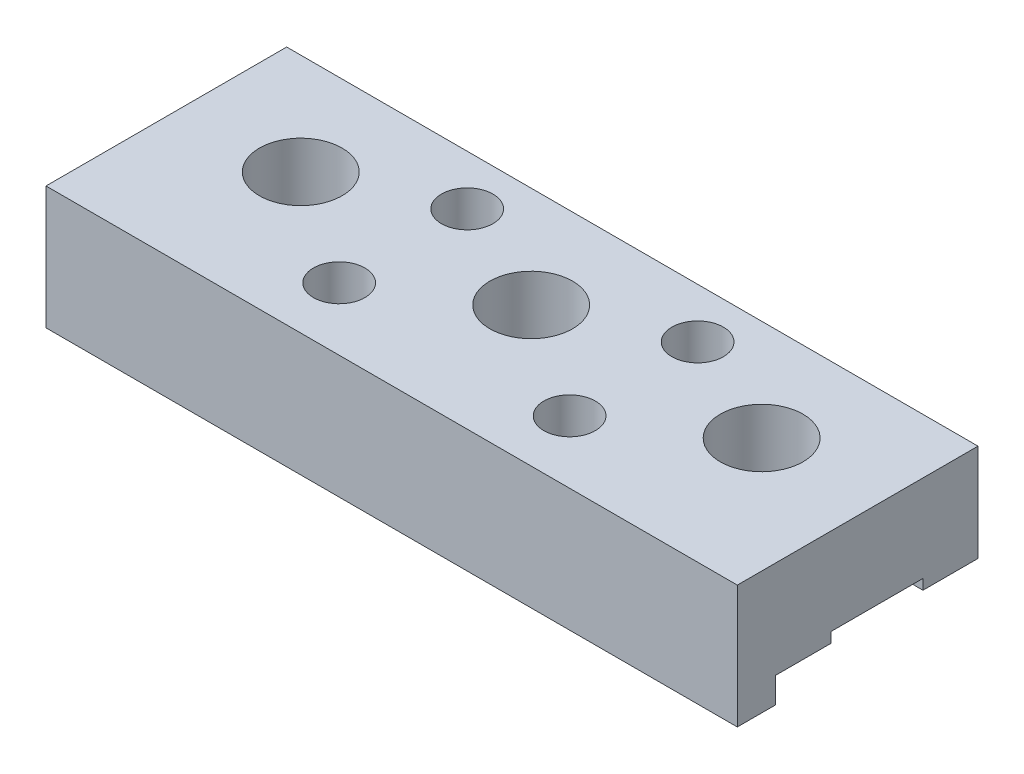
SolidWorks part; units mm, degrees
material "304 SSTL"
ref_plane "Front" through (0, 0, 0) normal (0, 0, 1) x (1, 0, 0)
ref_plane "Top" through (0, 0, 0) normal (0, 1, 0) x (1, 0, 0)
ref_plane "Right" through (0, 0, 0) normal (1, 0, 0) x (0, 0, -1)
sketch "Sketch1" plane through (0, 0, 0) normal (0, 1, 0) x (1, 0, 0)
  line L1 (-34.29, 11.43) -> (34.29, 11.43)
  line L2 (-34.29, 11.43) -> (-34.29, -11.43)
  line L3 (-34.29, -11.43) -> (34.29, -11.43)
  line L4 (34.29, 11.43) -> (34.29, -11.43)
  line L5 (-34.29, 11.43) -> (34.29, -11.43) construction
  line L6 (-34.29, -11.43) -> (34.29, 11.43) construction
  point P0 (0, 0)
  dimension "D1" = 68.58
  dimension "D2" = 22.86
extrude "Extrude1" add sketch "Sketch1" along normal blind 9.652
sketch "Sketch4" plane through (0, 9.652, 0) normal (0, 1, 0) x (1, 0, 0)
  line L0 (-34.29, 11.43) -> (-34.29, -11.43) construction
  line L1 (-34.29, -9.9822) -> (34.29, -9.9822)
  line L2 (-34.29, -9.9822) -> (-34.29, -13.7922)
  line L3 (-34.29, -13.7922) -> (34.29, -13.7922)
  line L4 (34.29, -9.9822) -> (34.29, -13.7922)
  line L5 (34.29, -11.43) -> (34.29, 11.43) construction
  line L6 (-34.29, -11.43) -> (34.29, -11.43) construction
  dimension "D1" = 1.4478
  dimension "D2" = 3.81
extrude "Extrude3" add sketch "Sketch4" against normal offset from surface (12.192 mm away) 2.54 up to face at (0, 0, 0) offset beyond the face yes
hole_wizard "5/16 Clearance Hole1" positions "3DSketch1" profile "Sketch2" hole size "5/16" standard "Ansi Inch" end condition through all
sketch3d "3DSketch1"
  line L2 (34.29, 0, 9.9822) -> (-34.29, 0, 9.9822) construction
  line L3 (-22.86, 0, -0.0508) -> (22.86, 0, -0.0508) construction
  line L5 (34.29, 0, -11.43) -> (-34.29, 0, -11.43) construction
  point P0 (-22.86, 0, -0.0508)
  point P2 (22.86, 0, -0.0508)
  point P21 (0, 0, -0.0508)
  point P24 (0, 0, -11.43)
  point P25 (0, 0, -0.0508)
  dimension "D1" = 45.72
  dimension "D3" = 10.033
sketch "Sketch2" plane through (-22.86, 0, -0.0508) normal (1, 0, 0) x (0, 0, -1)
  line L0 (0, 0) -> (0, 9.652)
  line L1 (0, 9.652) -> (4.1021, 9.652)
  line L2 (4.1021, 9.652) -> (4.1021, 0)
  line L5 (4.1021, 0) -> (0, 0)
  line L11 (0, -6.35) -> (0, 107.95) construction
  dimension "Thru Hole Dia." = 8.2042
  dimension "Thru Hole Depth" = 9.652
sketch "Sketch3" plane through (0, 0, 0) normal (0, -1, 0) x (1, 0, 0)
  line L0 (34.29, 9.9822) -> (34.29, -11.43) construction
  line L1 (-34.29, 4.5212) -> (34.29, 4.5212)
  line L2 (-34.29, 4.5212) -> (-34.29, -4.6228)
  line L3 (-34.29, -4.6228) -> (34.29, -4.6228)
  line L4 (34.29, 4.5212) -> (34.29, -4.6228)
  line L5 (-34.29, -0.0508) -> (34.29, -0.0508) construction
  circle A1 centre (22.86, -0.0508) radius 4.1021 construction
  circle A2 centre (22.86, -0.0508) radius 4.1021 construction
  point P0 (0, 0)
extrude "Extrude2" cut sketch "Sketch3" against normal blind 1.016
sketch "Sketch6" plane through (0, 0, 0) normal (0, -1, 0) x (1, 0, 0)
  line L0 (-34.29, -11.43) -> (-34.29, -4.6228) construction
  line L1 (34.29, -11.43) -> (-34.29, -11.43)
  line L2 (34.29, -11.43) -> (34.29, -10.0838)
  line L3 (34.29, -10.0838) -> (-34.29, -10.0838)
  line L4 (-34.29, -11.43) -> (-34.29, -10.0838)
  dimension "D1" = 1.3462
extrude "Cut-Extrude2" cut sketch "Sketch6" against normal through all
hole_wizard "1/4-20 Tapped Hole1" positions "Sketch8" profile "Sketch7" tap size "1/4-20" standard "Ansi Inch"
sketch "Sketch8" plane through (0, 9.652, 0) normal (0, 1, 0) x (-1, 0, 0)
  line L0 (34.29, 13.7922) -> (-34.29, 13.7922) construction
  point P0 (11.43, -5.1308)
  point P1 (11.43, 7.5692)
  point P3 (-11.43, 7.5692)
  point P5 (-11.43, -5.1308)
  dimension "D1" = 11.43
  dimension "D2" = 11.43
  dimension "D3" = 6.223
  dimension "D4" = 12.7
sketch "Sketch7" plane through (-11.43, 9.652, -5.1308) normal (1, 0, 0) x (0, 0, 1)
  line L0 (0, 0) -> (0, 20.5838)
  line L1 (0, 20.5838) -> (2.5527, 19.05)
  line L2 (2.5527, 19.05) -> (2.5527, 0)
  line L5 (2.5527, 0) -> (0, 0)
  line L10 (0, 20.5838) -> (-2.5527, 19.05) construction
  line L11 (0, -6.35) -> (0, 107.95) construction
  dimension "Tap Drill Dia." = 5.1054
  dimension "Tap Drill Depth" = 19.05
  dimension "Drill Angle" = 118
cosmetic thread "Hole Thread1" parameters "D1"=9.652, "D2"=6.35
cosmetic thread "Hole Thread2" parameters "D1"=12.192, "D2"=6.35
cosmetic thread "Hole Thread3" parameters "D1"=12.192, "D2"=6.35
cosmetic thread "Hole Thread4" parameters "D1"=9.652, "D2"=6.35
